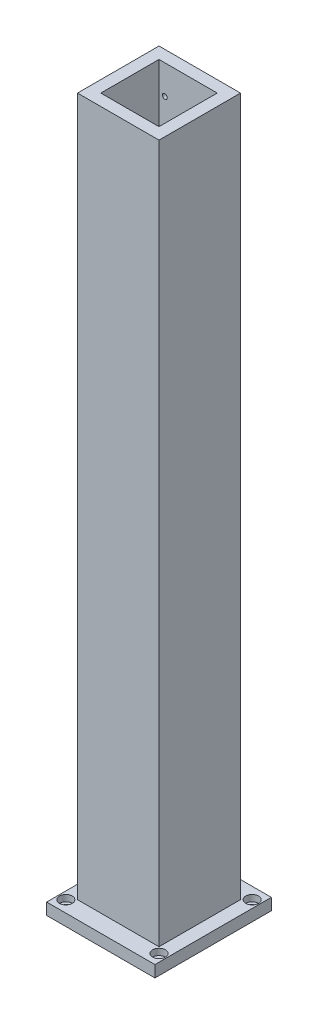
SolidWorks part; units mm, degrees
material "3003 Alloy"
ref_plane "Front Plane" through (0, 0, 0) normal (0, 0, 1) x (1, 0, 0)
ref_plane "Top Plane" through (0, 0, 0) normal (0, 1, 0) x (1, 0, 0)
ref_plane "Right Plane" through (0, 0, 0) normal (1, 0, 0) x (0, 0, -1)
sketch "Sketch1" plane through (0, 0, 0) normal (0, 1, 0) x (1, 0, 0)
  line L1 (-46.5, -50) -> (46.5, -50)
  line L2 (-46.5, -50) -> (-46.5, 50)
  line L3 (-46.5, 50) -> (46.5, 50)
  line L4 (46.5, -50) -> (46.5, 50)
  line L5 (-46.5, -50) -> (46.5, 50) construction
  line L6 (-46.5, 50) -> (46.5, -50) construction
  point P0 (0, 0)
  dimension "D1" = 93
  dimension "D2" = 100
extrude "Boss-Extrude1" add sketch "Sketch1" along normal blind 10
sketch "Sketch7" plane through (0, 10, 0) normal (0, 1, 0) x (1, 0, 0)
  line L0 (-35, 35) -> (35, 35)
  line L5 (-25, -25) -> (25, -25)
  line L6 (-25, -25) -> (-25, 25)
  line L11 (-25, 25) -> (25, 25)
  line L12 (25, -25) -> (25, 25)
  line L13 (-25, -25) -> (25, 25) construction
  line L14 (-25, 25) -> (25, -25) construction
  line L15 (35, -35) -> (35, 35)
  line L16 (-35, -35) -> (35, -35)
  line L17 (-35, -35) -> (-35, 35)
  point P0 (0, 0)
  dimension "D1" = 50
  dimension "D2" = 50
  dimension "D3" = 10
extrude "Boss-Extrude4" add sketch "Sketch7" along normal blind 600
sketch "Sketch8" plane through (0, 0, -35) normal (0, 0, -1) x (-1, 0, 0)
  line L0 (-20, 585) -> (20, 585) construction
  line L1 (20, 585) -> (20, 555) construction
  line L2 (20, 555) -> (-20, 555) construction
  line L3 (-20, 555) -> (-20, 585) construction
  line L4 (-35, 610) -> (35, 610) construction
  point P6 (0, 610)
  point P7 (0, 585)
  dimension "D1" = 25
  dimension "D2" = 40
  dimension "D3" = 30
hole_wizard "M5 Tapped Hole1" positions "Sketch9" profile "Sketch10" tap size "M5" standard "ISO"
sketch "Sketch9" plane through (0, 0, -35) normal (0, 0, -1) x (-1, 0, 0)
  point P0 (-20, 585)
  point P3 (20, 585)
  point P6 (20, 555)
  point P9 (-20, 555)
sketch "Sketch10" plane through (20, 585, -35) normal (1, 0, 0) x (0, 1, 0)
  line L0 (0, 0) -> (0, 13.6618)
  line L1 (0, 13.6618) -> (2.1, 12.4)
  line L2 (2.1, 12.4) -> (2.1, 0)
  line L5 (2.1, 0) -> (0, 0)
  line L10 (0, 13.6618) -> (-2.1, 12.4) construction
  line L11 (0, -6.35) -> (0, 107.95) construction
  dimension "Tap Drill Dia." = 4.2
  dimension "Tap Drill Depth" = 12.4
  dimension "Drill Angle" = 118
cosmetic thread "Hole Thread1" parameters "D1"=10, "D2"=5
cosmetic thread "Hole Thread2" parameters "D1"=10, "D2"=5
cosmetic thread "Hole Thread3" parameters "D1"=10, "D2"=5
cosmetic thread "Hole Thread4" parameters "D1"=10, "D2"=5
sketch "Sketch11" plane through (0, 10, 0) normal (0, 1, 0) x (1, 0, 0)
  line L0 (-40, 40) -> (40, 40) construction
  line L1 (40, 40) -> (40, -40) construction
  line L2 (40, -40) -> (-40, -40) construction
  line L3 (-40, -40) -> (-40, 40) construction
  line L4 (46.5, 50) -> (-46.5, 50) construction
  line L5 (-46.5, 50) -> (-46.5, -50) construction
  circle A0 centre (-40, 40) radius 2.75
  circle A1 centre (-40, -40) radius 2.75
  circle A2 centre (40, -40) radius 2.75
  circle A3 centre (40, 40) radius 2.75
  point P10 (0, 50)
  point P11 (0, 40)
  point P14 (-46.5, 0)
  point P15 (-40, 0)
  dimension "D3" = 5.5
  dimension "D1" = 80
  dimension "D2" = 80
extrude "Cut-Extrude1" cut sketch "Sketch11" against normal through all
sketch "Sketch12" plane through (0, 10, 0) normal (0, 1, 0) x (1, 0, 0)
  circle A0 centre (-40, 40) radius 5.5
  circle A1 centre (40, 40) radius 5.5
  circle A2 centre (40, -40) radius 5.5
  circle A3 centre (-40, -40) radius 5.5
  dimension "D1" = 11
extrude "Cut-Extrude2" cut sketch "Sketch12" against normal blind 5.5
